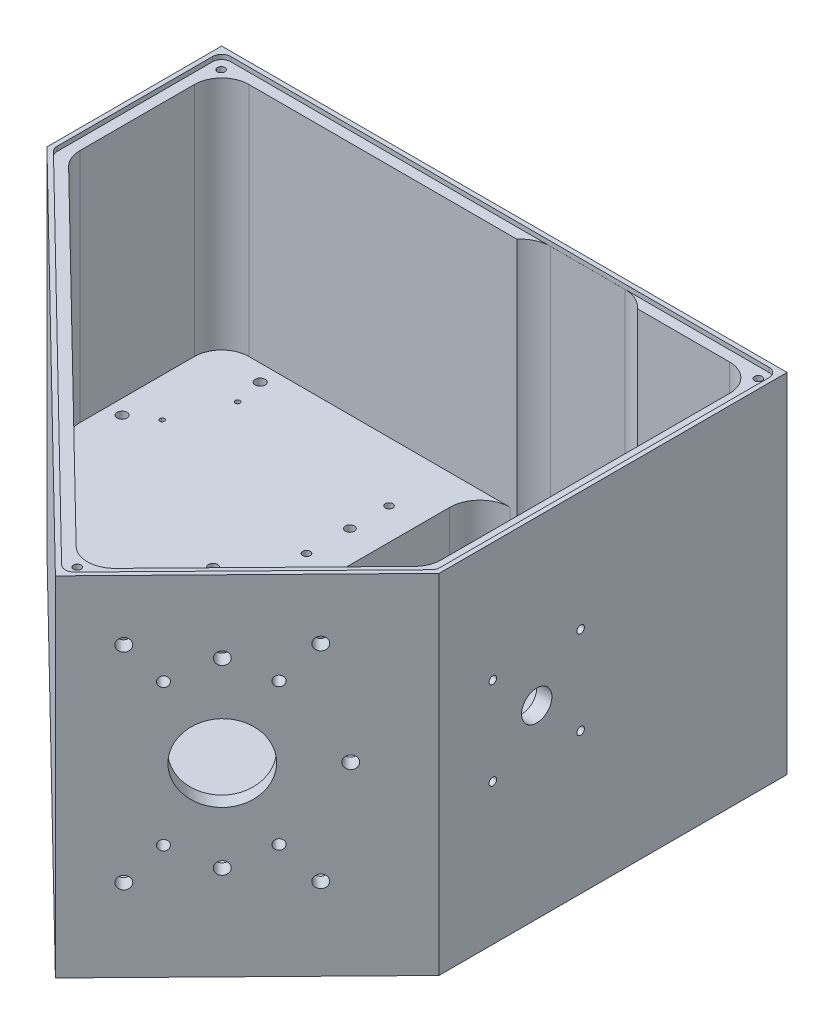
SolidWorks part; units mm, degrees
material "6061-T6 (SS)"
ref_plane "Front Plane" through (0, 0, 0) normal (0, 0, 1) x (1, 0, 0)
ref_plane "Top Plane" through (0, 0, 0) normal (0, 1, 0) x (1, 0, 0)
ref_plane "Right Plane" through (0, 0, 0) normal (1, 0, 0) x (0, 0, -1)
sketch "Sketch1" plane through (0, 0, 0) normal (0, 1, 0) x (1, 0, 0)
  line L5 (-99.4546, 85.2873) -> (-99.4546, 27.5807)
  line L6 (-99.4546, 27.5807) -> (24.6307, -93.7045)
  line L7 (24.6307, -93.7045) -> (87.2594, -29.6298)
  line L8 (87.2594, 85.2873) -> (87.2594, -29.6298)
  line L9 (-99.4546, 85.2873) -> (87.2594, 85.2873)
extrude "Boss-Extrude3" add sketch "Sketch1" along normal blind 10
sketch "Sketch6" plane through (0, 10, 0) normal (0, 1, 0) x (1, 0, 0)
  line L5 (-99.4546, 85.2873) -> (-99.4546, 27.5807)
  line L6 (-99.4546, 27.5807) -> (24.6307, -93.7045)
  line L7 (24.6307, -93.7045) -> (87.2594, -29.6298)
  line L8 (87.2594, -29.6298) -> (87.2594, 85.2873)
  line L9 (87.2594, 85.2873) -> (-99.4546, 85.2873)
  line L10 (82.2594, 80.2873) -> (-94.4546, 80.2873)
  line L11 (-94.4546, 80.2873) -> (-94.4546, 29.6853)
  line L12 (-94.4546, 29.6853) -> (24.55, -86.6339)
  line L13 (24.55, -86.6339) -> (82.2594, -27.5921)
  line L14 (82.2594, -27.5921) -> (82.2594, 80.2873)
  line L15 (82.2594, 80.2873) -> (-94.4546, 80.2873)
  line L16 (-94.4546, 80.2873) -> (-94.4546, 29.6853)
  line L17 (-94.4546, 29.6853) -> (24.55, -86.6339)
  line L18 (24.55, -86.6339) -> (82.2594, -27.5921)
  line L19 (82.2594, -27.5921) -> (82.2594, 80.2873)
  dimension "D1" = 5
extrude "Boss-Extrude5" add sketch "Sketch6" along normal blind 105
fillet "Fillet2" radius 9 5 edges at (82.2594, 62.5, 27.5921) (-94.4546, 62.5, -29.6853) (-94.4546, 62.5, -80.2873) (24.55, 62.5, 86.6339) (82.2594, 62.5, -80.2873)
sketch "Sketch9" plane through (0, 10, 0) normal (0, 1, 0) x (1, 0, 0)
  line L0 (-9.1641, 80.2873) -> (-9.1641, 16.2744)
  line L1 (73.2594, 80.2873) -> (-85.4546, 80.2873) construction
  line L2 (-9.1641, 16.2744) -> (-44.1325, -19.5013)
  line L3 (-91.7455, 27.0373) -> (18.1138, -80.3429) construction
  line L4 (-44.1325, -19.5013) -> (-96.3801, 31.5674)
  line L5 (-96.3801, 31.5674) -> (-96.3801, 80.2873)
  line L6 (-96.3801, 80.2873) -> (-9.1641, 80.2873)
extrude "Boss-Extrude7" add sketch "Sketch9" along normal blind 25.7
fillet "Fillet3" radius 10 1 edges at (-44.1325, 22.85, 19.5013)
fillet "Fillet4" radius 10 1 edges at (-9.1641, 22.85, -80.2873)
sketch "Sketch10" plane through (0, 115, 0) normal (0, 1, 0) x (1, 0, 0)
  line L10 (-97.9546, 28.2121) -> (24.6065, -91.5833)
  line L11 (24.6065, -91.5833) -> (85.7594, -29.0185)
  line L12 (85.7594, -29.0185) -> (85.7594, 83.7873)
  line L13 (85.7594, 83.7873) -> (-97.9546, 83.7873)
  line L14 (-97.9546, 83.7873) -> (-97.9546, 28.2121)
  line L15 (-97.9546, 28.2121) -> (24.6065, -91.5833)
  line L16 (24.6065, -91.5833) -> (85.7594, -29.0185)
  line L17 (85.7594, -29.0185) -> (85.7594, 83.7873)
  line L18 (85.7594, 83.7873) -> (-97.9546, 83.7873)
  line L19 (-97.9546, 83.7873) -> (-97.9546, 28.2121)
  dimension "D1" = 1.5
extrude "Cut-Extrude4" cut sketch "Sketch10" against normal blind 1.5
fillet "Fillet5" radius 3 5 edges at (-97.9546, 114.25, -83.7873) (-97.9546, 114.25, -28.2121) (85.7594, 114.25, -83.7873) (24.6065, 114.25, 91.5833) (85.7594, 114.25, 29.0185)
sketch "Sketch12" plane through (0, 0, 0) normal (0, -1, 0) x (1, 0, 0)
  line L0 (-86.0291, -30.2385) -> (-44.8318, 10.0291)
  line L1 (-44.8318, 10.0291) -> (-15.8869, -19.5841)
  line L2 (-15.8869, -19.5841) -> (-15.8869, -74.9478)
  line L3 (-15.8869, -74.9478) -> (-86.0291, -74.9478)
  line L4 (-86.0291, -74.9478) -> (-86.0291, -30.2385)
  line L5 (-91.7455, -27.0373) -> (-36.9812, 26.4912) construction
  line L6 (-37.1425, 12.35) -> (-9.1641, -16.2744) construction
extrude "Cut-Extrude5" cut sketch "Sketch12" against normal blind 20
fillet "Fillet6" radius 10 5 edges at (-86.0291, 10, -30.2385) (-44.8318, 10, 10.0291) (-15.8869, 10, -74.9478) (-15.8869, 10, -19.5841) (-86.0291, 10, -74.9478)
sketch "Sketch13" plane through (87.2594, 0, 0) normal (1, 0, 0) x (0, 0, -1)
  circle A0 centre (2.6126, 61.1) radius 5
  dimension "D1" = 10
extrude "Cut-Extrude6" cut sketch "Sketch13" against normal up to next
hole_wizard "M4x0.7 Tapped Hole2" positions "Sketch16" profile "Sketch17" tap size "M4x0.7" standard "ANSI Metric" end condition up to next
sketch "Sketch16" plane through (59.4364, 0, 58.0952) normal (0.7151, 0, 0.699) x (0.699, 0, -0.7151)
  point P0 (2.4311, 37.7673)
  point P6 (2.4311, 84.5327)
  point P9 (-24.5689, 84.5327)
  point P15 (-24.5689, 37.7673)
  point P27 (0, 0)
  point P28 (0, 0)
  point P29 (0, 0)
  point P30 (0, 0)
sketch "Sketch17" plane through (61.1358, 37.7673, 56.3566) normal (0, 1, 0) x (0.699, 0, -0.7151)
  line L0 (0, 0) -> (0, 5)
  line L1 (0, 5) -> (1.65, 5)
  line L2 (1.65, 5) -> (1.65, 0)
  line L5 (1.65, 0) -> (0, 0)
  line L11 (0, -6.35) -> (0, 107.95) construction
  dimension "Thru Tap Drill Dia." = 3.3
  dimension "Thru Tap Drill Depth" = 5
cosmetic thread "Hole Thread33" parameters "D2"=4
cosmetic thread "Hole Thread34" parameters "D2"=4
cosmetic thread "Hole Thread35" parameters "D2"=4
cosmetic thread "Hole Thread37" parameters "D2"=4
hole_wizard "SM1 Tapped Hole1" positions "Sketch19" profile "Sketch20" tap size "SM1" standard "UNS" end condition up to next
sketch "Sketch19" plane through (59.4364, 0, 58.0952) normal (0.7151, 0, 0.699) x (0.699, 0, -0.7151)
  point P0 (-10.8259, 61.15)
  point P3 (0, 0)
sketch "Sketch20" plane through (51.8692, 61.15, 65.8371) normal (0, 1, 0) x (0.699, 0, -0.7151)
  line L0 (0, 0) -> (0, 5)
  line L1 (0, 5) -> (12.7, 5)
  line L2 (12.7, 5) -> (12.7, 0)
  line L5 (12.7, 0) -> (0, 0)
  line L11 (0, -6.35) -> (0, 107.95) construction
  dimension "Thru Tap Drill Dia." = 25.4
  dimension "Thru Tap Drill Depth" = 5
cosmetic thread "Hole Thread17" parameters "D1"=5, "D2"=26.4
hole_wizard "M4x0.7 Tapped Hole1" positions "Sketch21" profile "Sketch22" tap size "M4x0.7" standard "ANSI Metric"
sketch "Sketch21" plane through (0, 35.7, 0) normal (0, 1, 0) x (1, 0, 0)
  point P0 (-76.2504, 74.821)
  point P3 (-89.6156, 42.5545)
sketch "Sketch22" plane through (-76.2504, 35.7, -74.821) normal (1, 0, 0) x (0, 0, 1)
  line L0 (0, 0) -> (0, 8.9914)
  line L1 (0, 8.9914) -> (1.65, 8)
  line L2 (1.65, 8) -> (1.65, 0)
  line L5 (1.65, 0) -> (0, 0)
  line L10 (0, 8.9914) -> (-1.65, 8) construction
  line L11 (0, -6.35) -> (0, 107.95) construction
  dimension "Tap Drill Dia." = 3.3
  dimension "Tap Drill Depth" = 8
  dimension "Drill Angle" = 118
cosmetic thread "Hole Thread18" parameters "D1"=8, "D2"=4
cosmetic thread "Hole Thread19" parameters "D1"=8, "D2"=4
hole_wizard "M2x0.4 Tapped Hole1" positions "Sketch27" profile "Sketch28" tap size "M2x0.4" standard "ANSI Metric"
sketch "Sketch27" plane through (0, 10, 0) normal (0, 1, 0) x (1, 0, 0)
  point P0 (5.7896, 54.3126)
  point P3 (25.7896, 54.3126)
  point P6 (5.7896, 34.3126)
  point P9 (25.7896, 34.3126)
sketch "Sketch28" plane through (5.7896, 10, -54.3126) normal (1, 0, 0) x (0, 0, 1)
  line L0 (0, 0) -> (0, 5.6807)
  line L1 (0, 5.6807) -> (0.8, 5.2)
  line L2 (0.8, 5.2) -> (0.8, 0)
  line L5 (0.8, 0) -> (0, 0)
  line L10 (0, 5.6807) -> (-0.8, 5.2) construction
  line L11 (0, -6.35) -> (0, 107.95) construction
  dimension "Tap Drill Dia." = 1.6
  dimension "Tap Drill Depth" = 5.2
  dimension "Drill Angle" = 118
cosmetic thread "Hole Thread12" parameters "D1"=4, "D2"=2
cosmetic thread "Hole Thread13" parameters "D1"=4, "D2"=2
cosmetic thread "Hole Thread14" parameters "D1"=4, "D2"=2
cosmetic thread "Hole Thread15" parameters "D1"=4, "D2"=2
hole_wizard "M3x0.5 Tapped Hole1" positions "Sketch29" profile "Sketch30" tap size "M3x0.5" standard "ANSI Metric"
sketch "Sketch29" plane through (0, 10, 0) normal (0, 1, 0) x (1, 0, 0)
  point P0 (53.4865, 36.7407)
  point P3 (53.4865, 17.3387)
sketch "Sketch30" plane through (53.4865, 10, -36.7407) normal (1, 0, 0) x (0, 0, 1)
  line L0 (0, 0) -> (0, 8.2511)
  line L1 (0, 8.2511) -> (1.25, 7.5)
  line L2 (1.25, 7.5) -> (1.25, 0)
  line L5 (1.25, 0) -> (0, 0)
  line L10 (0, 8.2511) -> (-1.25, 7.5) construction
  line L11 (0, -6.35) -> (0, 107.95) construction
  dimension "Tap Drill Dia." = 2.5
  dimension "Tap Drill Depth" = 7.5
  dimension "Drill Angle" = 118
cosmetic thread "Hole Thread20" parameters "D1"=6, "D2"=3
cosmetic thread "Hole Thread21" parameters "D1"=6, "D2"=3
hole_wizard "Ø3.0mm Dowel Hole1" positions "Sketch31" profile "Sketch32" hole size "Ø3.0" standard "ANSI Metric"
sketch "Sketch31" plane through (0, 10, 0) normal (0, 1, 0) x (1, 0, 0)
  point P0 (73.9865, 2.3387)
  point P3 (53.4865, 53.3387)
sketch "Sketch32" plane through (73.9865, 10, -2.3387) normal (1, 0, 0) x (0, 0, 1)
  line L0 (0, 0) -> (0, 6.1013)
  line L1 (0, 6.1013) -> (1.5, 5.2)
  line L2 (1.5, 5.2) -> (1.5, 0)
  line L5 (1.5, 0) -> (0, 0)
  line L10 (0, 6.1013) -> (-1.5, 5.2) construction
  line L11 (0, -6.35) -> (0, 107.95) construction
  dimension "Hole Dia." = 3
  dimension "Hole Depth" = 5.2
  dimension "Drill Angle" = 118
hole_wizard "M3x0.5 Tapped Hole2" positions "Sketch33" profile "Sketch34" tap size "M3x0.5" standard "ANSI Metric" end condition up to next
sketch "Sketch33" plane through (87.2594, 0, 0) normal (1, 0, 0) x (0, 0, -1)
  point P0 (17.1126, 75.6)
  point P3 (17.1126, 46.6)
  point P6 (-11.8874, 46.6)
  point P9 (-11.8874, 75.6)
sketch "Sketch34" plane through (87.2594, 75.6, -17.1126) normal (0, 1, 0) x (0, 0, -1)
  line L0 (0, 0) -> (0, 5)
  line L1 (0, 5) -> (1.25, 5)
  line L2 (1.25, 5) -> (1.25, 0)
  line L5 (1.25, 0) -> (0, 0)
  line L11 (0, -6.35) -> (0, 107.95) construction
  dimension "Thru Tap Drill Dia." = 2.5
  dimension "Thru Tap Drill Depth" = 5
cosmetic thread "Hole Thread22" parameters "D2"=3
cosmetic thread "Hole Thread23" parameters "D2"=3
cosmetic thread "Hole Thread24" parameters "D2"=3
cosmetic thread "Hole Thread25" parameters "D2"=3
hole_wizard "M3x0.5 Tapped Hole3" positions "Sketch35" profile "Sketch36" tap size "M3x0.5" standard "ANSI Metric"
sketch "Sketch35" plane through (0, 35.7, 0) normal (0, 1, 0) x (1, 0, 0)
  point P0 (-19.6019, 60.7185)
  point P3 (-19.6019, 33.4561)
sketch "Sketch36" plane through (-19.6019, 35.7, -60.7185) normal (1, 0, 0) x (0, 0, 1)
  line L0 (0, 0) -> (0, 8.2511)
  line L1 (0, 8.2511) -> (1.25, 7.5)
  line L2 (1.25, 7.5) -> (1.25, 0)
  line L5 (1.25, 0) -> (0, 0)
  line L10 (0, 8.2511) -> (-1.25, 7.5) construction
  line L11 (0, -6.35) -> (0, 107.95) construction
  dimension "Tap Drill Dia." = 2.5
  dimension "Tap Drill Depth" = 7.5
  dimension "Drill Angle" = 118
cosmetic thread "Hole Thread26" parameters "D1"=6, "D2"=3
cosmetic thread "Hole Thread27" parameters "D1"=6, "D2"=3
hole_wizard "1/16 (0.0625) Dowel Hole1" positions "Sketch37" profile "Sketch38" hole size "1/16" standard "ANSI Inch"
sketch "Sketch37" plane through (0, 35.7, 0) normal (0, 1, 0) x (1, 0, 0)
  point P0 (-81.6501, 47.8466)
  point P3 (-74.36, 65.4465)
sketch "Sketch38" plane through (-81.6501, 35.7, -47.8466) normal (1, 0, 0) x (0, 0, 1)
  line L0 (0, 0) -> (0, 5.6769)
  line L1 (0, 5.6769) -> (0.7937, 5.2)
  line L2 (0.7937, 5.2) -> (0.7937, 0)
  line L5 (0.7937, 0) -> (0, 0)
  line L10 (0, 5.6769) -> (-0.7938, 5.2) construction
  line L11 (0, -6.35) -> (0, 107.95) construction
  dimension "Hole Dia." = 1.5875
  dimension "Hole Depth" = 5.2
  dimension "Drill Angle" = 118
hole_wizard "Ø3.0mm Dowel Hole2" positions "Sketch39" profile "Sketch40" hole size "Ø3.0" standard "ANSI Metric"
sketch "Sketch39" plane through (0, 35.7, 0) normal (0, 1, 0) x (1, 0, 0)
  point P0 (-19.5752, 47.747)
  point P3 (-31.1617, 14.1671)
sketch "Sketch40" plane through (-19.5752, 35.7, -47.747) normal (1, 0, 0) x (0, 0, 1)
  line L0 (0, 0) -> (0, 6.1013)
  line L1 (0, 6.1013) -> (1.5, 5.2)
  line L2 (1.5, 5.2) -> (1.5, 0)
  line L5 (1.5, 0) -> (0, 0)
  line L10 (0, 6.1013) -> (-1.5, 5.2) construction
  line L11 (0, -6.35) -> (0, 107.95) construction
  dimension "Hole Dia." = 3
  dimension "Hole Depth" = 5.2
  dimension "Drill Angle" = 118
hole_wizard "M3x0.5 Tapped Hole4" positions "Sketch41" profile "Sketch42" tap size "M3x0.5" standard "ANSI Metric"
sketch "Sketch41" plane through (0, 113.5, 0) normal (0, 1, 0) x (1, 0, 0)
  point P0 (-94.2739, 79.9332)
  point P2 (82.766, 80.2873)
  point P4 (24.2405, -86.105)
sketch "Sketch42" plane through (-94.2739, 113.5, -79.9332) normal (1, 0, 0) x (0, 0, 1)
  line L0 (0, 0) -> (0, 8.2511)
  line L1 (0, 8.2511) -> (1.25, 7.5)
  line L2 (1.25, 7.5) -> (1.25, 0)
  line L5 (1.25, 0) -> (0, 0)
  line L10 (0, 8.2511) -> (-1.25, 7.5) construction
  line L11 (0, -6.35) -> (0, 107.95) construction
  dimension "Tap Drill Dia." = 2.5
  dimension "Tap Drill Depth" = 7.5
  dimension "Drill Angle" = 118
cosmetic thread "Hole Thread28" parameters "D1"=6, "D2"=3
cosmetic thread "Hole Thread29" parameters "D1"=6, "D2"=3
cosmetic thread "Hole Thread30" parameters "D1"=6, "D2"=3
ref_plane "Plane1" through (82.7594, 113.5, -83.7873) normal (-1, 0, 0) x (0, 0, 1)
sketch "Sketch44" plane through (0, 113.5, 0) normal (0, 1, 0) x (1, 0, 0)
  line L0 (10.5811, 73.7772) -> (35.2342, 73.7772) construction
  line L1 (10.5811, 83.7772) -> (35.2342, 83.7772)
  line L2 (10.5811, 63.7772) -> (35.2342, 63.7772)
  arc A0 (10.5811, 83.7772) -> (10.5811, 63.7772) centre (10.5811, 73.7772) ccw
  arc A1 (35.2342, 63.7772) -> (35.2342, 83.7772) centre (35.2342, 73.7772) ccw
  point P2 (22.9077, 73.7772)
  dimension "D1" = 10
extrude "Cut-Extrude7" cut sketch "Sketch44" against normal up to surface (103.5 mm away) up to face at (73.9865, 10, -0.8387)
hole_wizard "M5x0.8 Tapped Hole2" positions "Sketch45" profile "Sketch46" tap size "M5x0.8" standard "ANSI Metric" end condition up to next
sketch "Sketch45" plane through (59.4364, 0, 58.0952) normal (0.7151, 0, 0.699) x (0.699, 0, -0.7151)
  circle A1 centre (-10.8259, 61.15) radius 12.7 construction
  point P0 (-10.8259, 91.15)
  point P2 (-10.8259, 31.15)
  point P4 (19.1741, 61.15)
  point P8 (0, 0)
  point P15 (0, 0)
  dimension "D3" = 30
  dimension "D1" = 30
  dimension "D2" = 60
  dimension "D4" = 30
sketch "Sketch46" plane through (51.8692, 91.15, 65.8371) normal (0, 1, 0) x (0.699, 0, -0.7151)
  line L0 (0, 0) -> (0, 5)
  line L1 (0, 5) -> (2.1, 5)
  line L2 (2.1, 5) -> (2.1, 0)
  line L5 (2.1, 0) -> (0, 0)
  line L11 (0, -6.35) -> (0, 107.95) construction
  dimension "Thru Tap Drill Dia." = 4.2
  dimension "Thru Tap Drill Depth" = 5
cosmetic thread "Hole Thread38" parameters "D2"=5
cosmetic thread "Hole Thread39" parameters "D2"=5
cosmetic thread "Hole Thread40" parameters "D2"=5
hole_wizard "M5x0.8 Tapped Hole3" positions "Sketch47" profile "Sketch48" tap size "M5x0.8" standard "ANSI Metric" end condition up to next
sketch "Sketch47" plane through (59.4364, 0, 58.0952) normal (0.7151, 0, 0.699) x (0.699, 0, -0.7151)
  point P0 (-33.8259, 95.15)
  point P2 (12.1741, 95.15)
  point P4 (12.1741, 27.15)
  point P6 (-33.8259, 27.15)
  point P9 (0, 0)
  point P10 (0, 0)
  point P11 (0, 0)
  point P16 (13.3112, 100.6148)
  point P17 (0, 0)
  dimension "D1" = 46
  dimension "D2" = 68
  dimension "D3" = 34
  dimension "D4" = 23
sketch "Sketch48" plane through (35.7924, 95.15, 82.2851) normal (0, 1, 0) x (0.699, 0, -0.7151)
  line L0 (0, 0) -> (0, 5)
  line L1 (0, 5) -> (2.1, 5)
  line L2 (2.1, 5) -> (2.1, 0)
  line L5 (2.1, 0) -> (0, 0)
  line L11 (0, -6.35) -> (0, 107.95) construction
  dimension "Thru Tap Drill Dia." = 4.2
  dimension "Thru Tap Drill Depth" = 5
cosmetic thread "Hole Thread41" parameters "D2"=5
cosmetic thread "Hole Thread42" parameters "D2"=5
cosmetic thread "Hole Thread43" parameters "D2"=5
cosmetic thread "Hole Thread44" parameters "D2"=5
